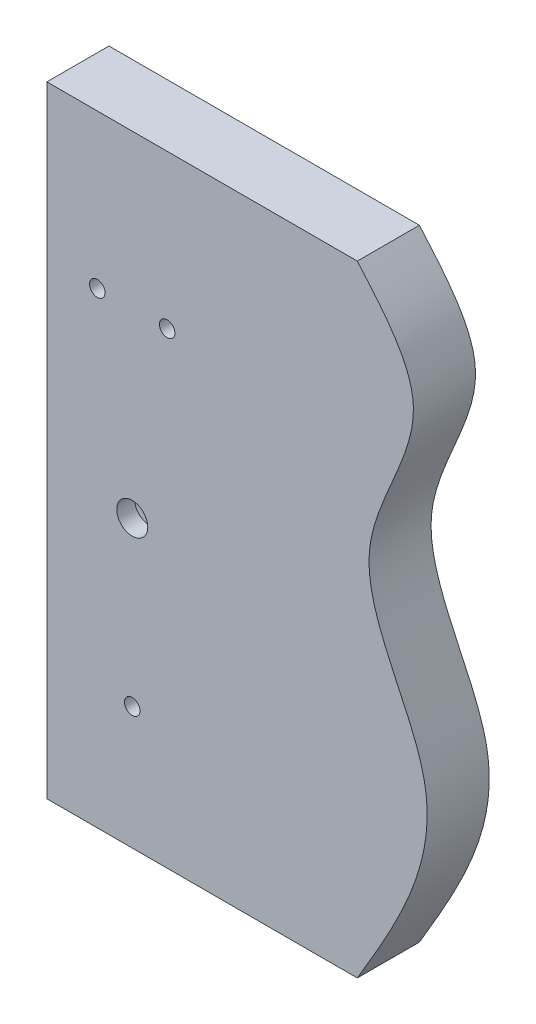
SolidWorks part; units mm, degrees
material "Chêne"
ref_plane "Face" through (0, 0, 0) normal (0, 0, 1) x (1, 0, 0)
ref_plane "Dessus" through (0, 0, 0) normal (0, 1, 0) x (1, 0, 0)
ref_plane "Droite" through (0, 0, 0) normal (1, 0, 0) x (0, 0, -1)
sketch "Esquisse1" plane through (0, 0, 0) normal (0, 0, 1) x (1, 0, 0)
  line L0 (0, 0) -> (0, 57.0464) construction
  line L1 (-150, 200) -> (50, 200)
  line L2 (-150, 200) -> (-150, -200)
  line L3 (-150, -200) -> (50, -200)
  line L5 (0, 0) -> (65.7907, 0) construction
  spline S0 degree 3 poles (50, 200) (66.8796, 180.5626) (108.794, 132.2966) (27.2783, 35.2366) (123.4738, -75.9938) (75.8926, -156.2995) (50, -200) knots 0 0 0 0 0.163804 0.406749 0.677167 1 1 1 1
  dimension "D1" = 200
  dimension "D2" = 400
extrude "Extrusion1" add sketch "Esquisse1" along normal mid plane 40
sketch "Esquisse2" plane through (-150, 0, 0) normal (-1, 0, 0) x (0, 0, 1)
  line L0 (0, 0) -> (0, 41.3685) construction
  line L1 (-11, 80) -> (11, 80)
  line L2 (-11, 80) -> (-11, -150)
  line L3 (-11, -150) -> (11, -150)
  line L4 (11, 80) -> (11, -150)
  line L5 (0, 41.3685) -> (0, 0) construction
  line L6 (0, 0) -> (40.4435, 0) construction
  line L7 (20, 200) -> (-20, 200) construction
  point P7 (0, 200)
  dimension "D1" = 230
  dimension "D2" = 22
  dimension "D3" = 120
extrude "Enlèv. mat.-Extru.1" cut sketch "Esquisse2" against normal blind 3
sketch "Esquisse3" plane through (37.1525, -36.3213, 0) normal (0, 0, 1) x (0, 1, 0)
  line L0 (236.3213, 187.1525) -> (-163.6787, 187.1525) construction
  line L1 (-80.1787, 184.1525) -> (82.8213, 184.1525)
  line L2 (-80.1787, 184.1525) -> (-80.1787, 107.1525)
  line L3 (-80.1787, 107.1525) -> (82.8213, 107.1525)
  line L4 (82.8213, 184.1525) -> (82.8213, 107.1525)
  line L7 (36.3213, 37.1525) -> (36.3213, -86.8563) construction
  line L8 (236.3213, -12.8475) -> (236.3213, 187.1525) construction
  line L9 (-163.6787, 187.1525) -> (-163.6787, -12.8475) construction
  dimension "D1" = 163
  dimension "D2" = 77
  dimension "D3" = 3
  dimension "D4" = 153.5
extrude "Enlèv. mat.-Extru.2" cut sketch "Esquisse3" against normal mid plane 17
sketch "Esquisse4" plane through (0, 0, 20) normal (0, 0, 1) x (1, 0, 0)
  line L1 (-150, 200) -> (-150, -200) construction
  line L2 (50, 200) -> (-150, 200) construction
  line L3 (-95, -16) -> (-95, 156.6738) construction
  circle A0 centre (-95, -16) radius 10
  circle A1 centre (-117.5, 101) radius 5
  circle A2 centre (-95, -121) radius 5
  circle A3 centre (-72.5, 101) radius 5
  dimension "D3" = 20
  dimension "D4" = 10
  dimension "D5" = 10
  dimension "D9" = 10
  dimension "D1" = 55
  dimension "D2" = 216
  dimension "D6" = 117
  dimension "D7" = 105
  dimension "D8" = 22.5
extrude "Enlèv. mat.-Extru.3" cut sketch "Esquisse4" against normal through all
